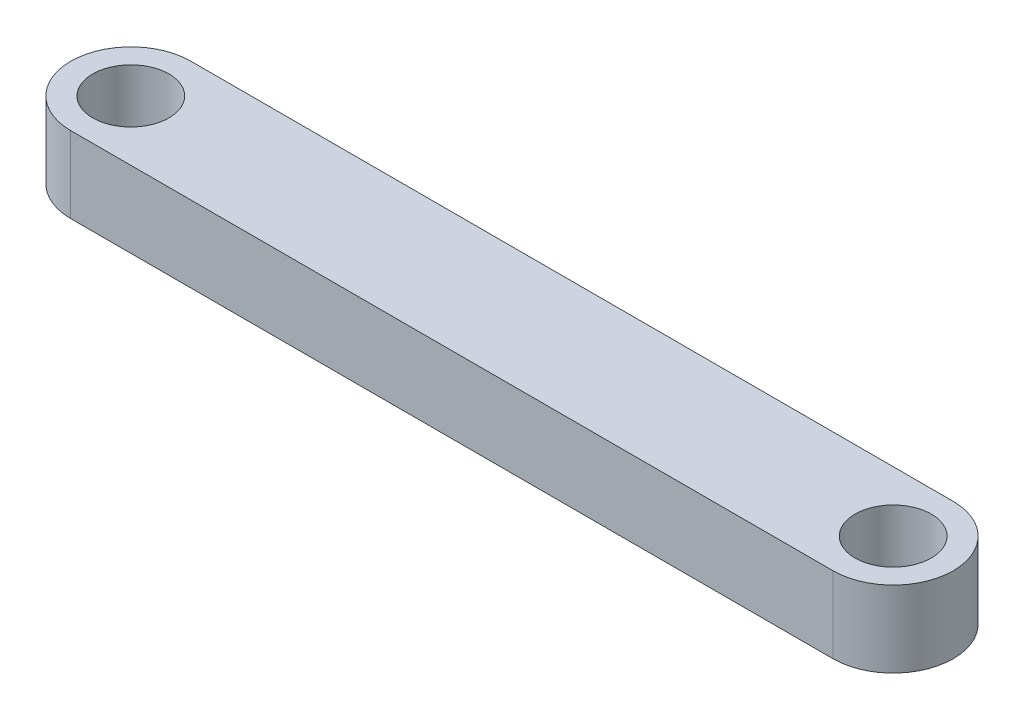
SolidWorks part; units mm, degrees
ref_plane "Front Plane" through (0, 0, 0) normal (0, 0, 1) x (1, 0, 0)
ref_plane "Top Plane" through (0, 0, 0) normal (0, 1, 0) x (1, 0, 0)
ref_plane "Right Plane" through (0, 0, 0) normal (1, 0, 0) x (0, 0, -1)
sketch "Sketch1" plane through (0, 0, 0) normal (0, 1, 0) x (1, 0, 0)
  line L0 (-15, 2.365) -> (-15, -2.365) construction
  line L1 (-15, -2.365) -> (15, -2.365)
  line L2 (0, 0) -> (0, -4.7138) construction
  line L3 (-15, 2.365) -> (15, 2.365)
  line L4 (13.5657, 0) -> (21.1495, 0) construction
  line L5 (-15, -2.365) -> (0, 0) construction
  line L6 (-15, 2.365) -> (0, 0) construction
  line L7 (-13.5657, 0) -> (-21.1495, 0) construction
  line L8 (-15, -2.365) -> (-15.756, -1.7727)
  line L9 (0, 0) -> (0, 3.3498) construction
  line L10 (15, 2.365) -> (0, 0) construction
  line L11 (15, -2.365) -> (0, 0) construction
  line L12 (15, -2.365) -> (15.756, -1.7727)
  line L13 (15, 2.365) -> (15.756, 1.7727)
  circle A0 centre (15, 0) radius 1.5
  arc A1 (-15, 2.365) -> (-15, -2.365) centre (-15, 0) ccw
  circle A2 centre (-15, 0) radius 1.5
  arc A3 (15, 2.365) -> (15, -2.365) centre (15, 0) cw
  point P0 (0, 0)
  point P6 (0, -2.365)
  point P9 (-15, 0)
  point P28 (0, 2.365)
  dimension "D1" = 30
  dimension "D2" = 3
extrude "Boss-Extrude1" add sketch "Sketch1" along normal blind 3
